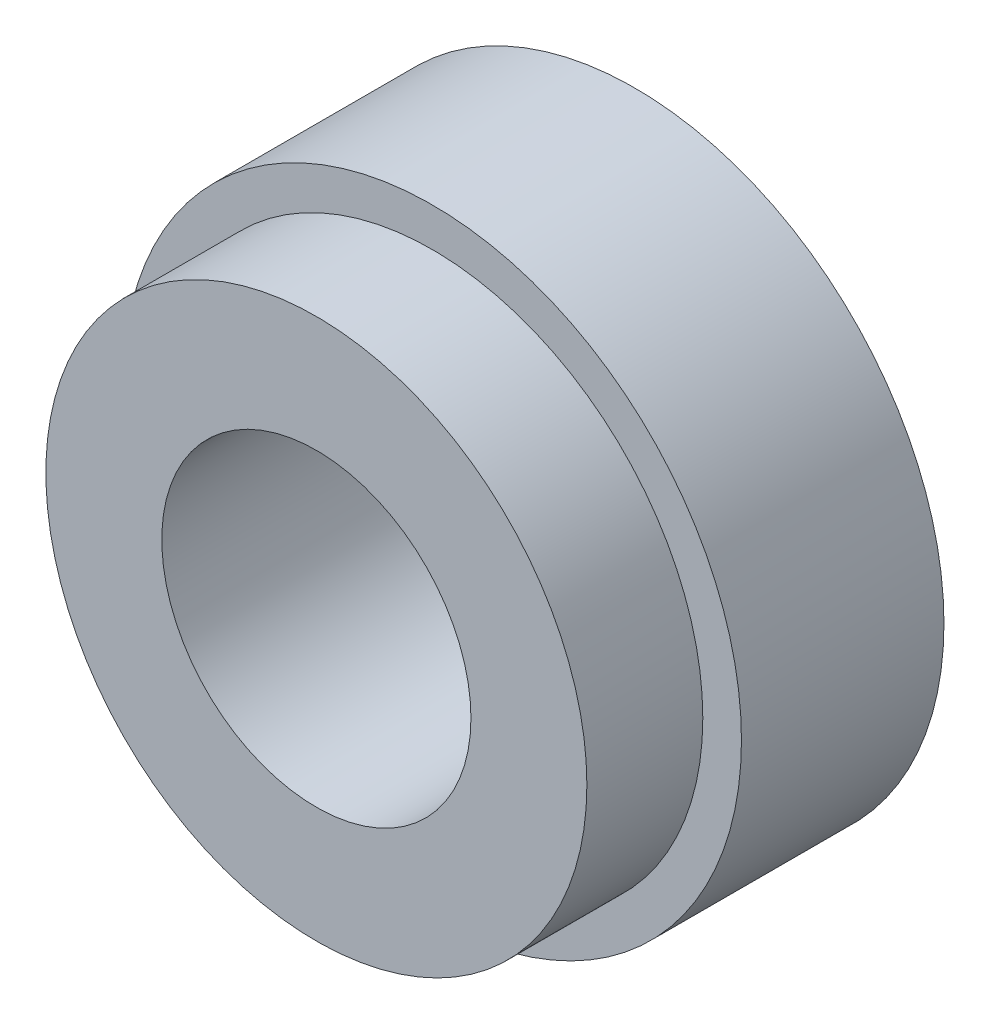
SolidWorks part; units mm, degrees
ref_plane "Front Plane" through (0, 0, 0) normal (0, 0, 1) x (1, 0, 0)
ref_plane "Top Plane" through (0, 0, 0) normal (0, 1, 0) x (1, 0, 0)
ref_plane "Right Plane" through (0, 0, 0) normal (1, 0, 0) x (0, 0, -1)
sketch "Sketch1" plane through (0, 0, 0) normal (0, 0, 1) x (1, 0, 0)
  circle A0 centre (0, 0) radius 50.8
extrude "Boss-Extrude1" add sketch "Sketch1" along normal blind 33.274
sketch "Sketch3" plane through (0, 0, 33.274) normal (0, 0, 1) x (1, 0, 0)
  circle A0 centre (0, 0) radius 44.45
extrude "Boss-Extrude2" add sketch "Sketch3" along normal blind 19.05
sketch "Sketch5" plane through (0, 0, 0) normal (0, 0, 1) x (1, 0, 0)
  circle A0 centre (0, 0) radius 25.4
extrude "Cut-Extrude1" cut sketch "Sketch5" along normal through all
ref_plane "Plane1" through (0, 0, 3.048) normal (0, 0, 1) x (1, 0, 0)
sketch "Sketch10" plane through (0, 0, 3.048) normal (0, 0, 1) x (1, 0, 0)
  line L0 (0, 0) -> (77.9486, 45.0037) construction
  line L1 (0, -50.8) -> (83.9402, -50.8) construction
  line L2 (0, -28.7782) -> (0, 28.7782) construction
  circle A0 centre (0, 0) radius 50.8 construction
